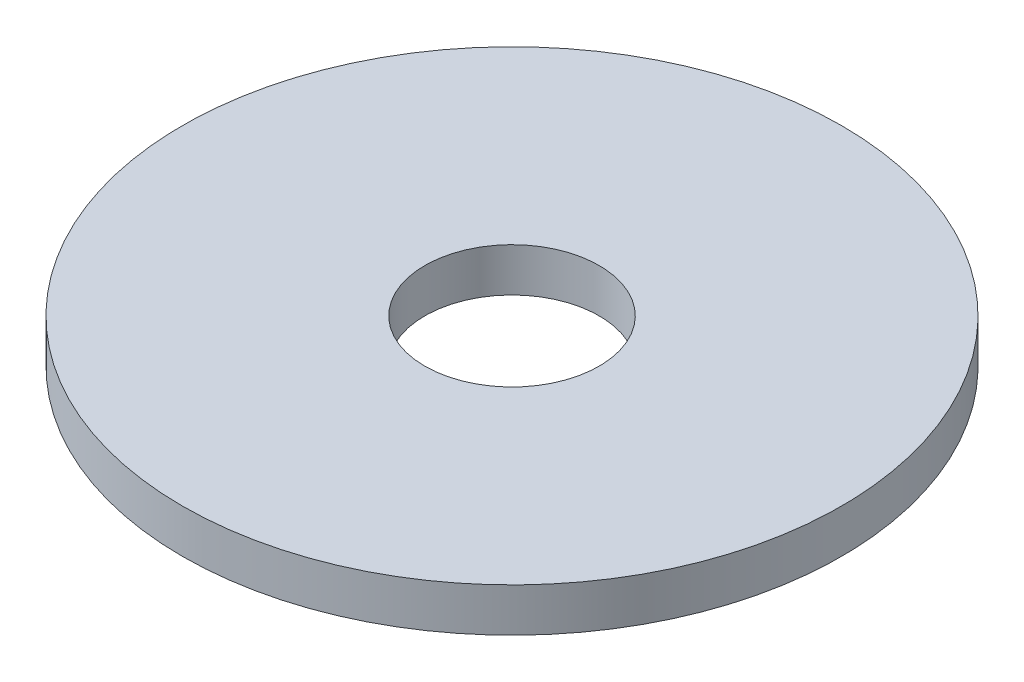
SolidWorks part; units mm, degrees
material "PTFE (general)"
ref_plane "Front Plane" through (0, 0, 0) normal (0, 0, 1) x (1, 0, 0)
ref_plane "Top Plane" through (0, 0, 0) normal (0, 1, 0) x (1, 0, 0)
ref_plane "Right Plane" through (0, 0, 0) normal (1, 0, 0) x (0, 0, -1)
sketch "Sketch1" plane through (0, 0, 0) normal (0, 1, 0) x (1, 0, 0)
  circle A0 centre (0, 0) radius 6
  circle A1 centre (0, 0) radius 1.5875
  dimension "D1" = 12
  dimension "D2" = 3.175
extrude "Boss-Extrude1" add sketch "Sketch1" along normal blind 0.7937
